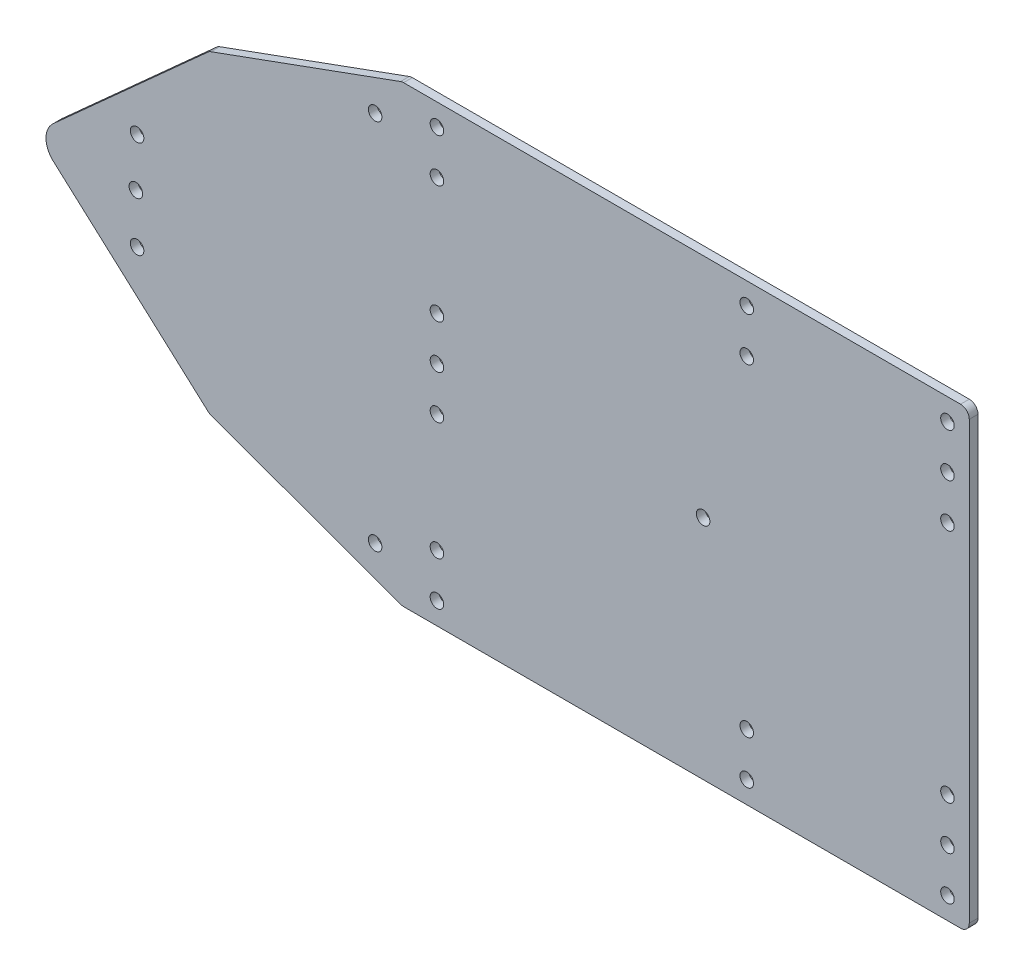
SolidWorks part; units mm, degrees
material "环氧板3240"
ref_plane "前视基准面" through (0, 0, 0) normal (0, 0, 1) x (1, 0, 0)
ref_plane "上视基准面" through (0, 0, 0) normal (0, 1, 0) x (1, 0, 0)
ref_plane "右视基准面" through (0, 0, 0) normal (1, 0, 0) x (0, 0, -1)
other "Configuration Table"
sketch "草图1" plane through (0, 0, 0) normal (0, 0, 1) x (1, 0, 0)
  line L0 (387.2013, -62.8358) -> (387.2013, 41.1642)
  line L1 (387.2013, 41.1642) -> (257.2013, 41.1642)
  line L2 (257.2013, 41.1642) -> (213.0357, 25.0892)
  line L4 (173.1369, -10.8358) -> (387.2013, -10.8358) construction
  line L5 (387.2013, -62.8358) -> (257.2013, -62.8358)
  line L6 (257.2013, -62.8358) -> (213.0357, -46.7609)
  line L8 (213.0357, 25.0892) -> (173.1369, -10.8358)
  line L9 (173.1369, -10.8358) -> (213.0357, -46.7609)
  dimension "D1" = 104
  dimension "D2" = 130
  dimension "D3" = 47
  dimension "D4" = 158
  dimension "D5" = 160
extrude "凸台-拉伸1" add sketch "草图1" along normal blind 2
fillet "圆角1" radius 5 1 edges at (173.1369, -10.8358, 1)
fillet "圆角2" radius 2 6 edges at (387.2013, 41.1642, 1) (257.2013, 41.1642, 1) (213.0357, 25.0892, 1) (213.0357, -46.7609, 1) (257.2013, -62.8358, 1) (387.2013, -62.8358, 1)
sketch "草图2" plane through (0, 0, 0) normal (0, 0, -1) x (-1, 0, 0)
  line L0 (-387.2013, 36.1642) -> (-243.4639, 36.1642) construction
  line L1 (-387.2013, -60.8358) -> (-387.2013, 39.1642) construction
  line L2 (-256.8699, 41.0436) -> (-213.401, 25.2222) construction
  line L3 (-385.2013, 41.1642) -> (-257.5539, 41.1642) construction
  line L4 (-387.2013, -10.8358) -> (-175.6093, -10.8358) construction
  line L5 (-382.2013, 36.1642) -> (-382.2013, -10.8358) construction
  line L6 (-258.541, 36.1642) -> (-177.1346, -10.8358) construction
  line L7 (-265.2013, 36.1642) -> (-265.2013, -10.8358) construction
  line L8 (-336.2013, 36.1642) -> (-336.2013, -10.8358) construction
  line L9 (-257.2013, 41.1642) -> (-183.864, -1.1771) construction
  line L10 (-251.041, 31.8341) -> (-248.541, 36.1642) construction
  line L11 (-212.7468, 24.8291) -> (-177.2636, -7.1201) construction
  circle A1 centre (-265.2013, 36.1642) radius 1.55
  circle A2 centre (-251.041, 31.8341) radius 1.55
  arc A3 (-177.2636, -14.5515) -> (-177.2636, -7.1201) centre (-180.6093, -10.8358) ccw construction
  circle A4 centre (-336.2013, 26.1642) radius 1.55
  circle A6 centre (-265.2013, 26.1642) radius 1.55
  circle A7 centre (-265.2013, -0.8358) radius 1.55
  circle A10 centre (-382.2013, 36.1642) radius 1.55
  circle A11 centre (-382.2013, 26.1642) radius 1.55
  circle A12 centre (-196.4814, 0.3341) radius 1.55
  circle A13 centre (-326.2013, -10.8358) radius 1.55
  circle A14 centre (-196.2013, -10.8358) radius 1.55
  circle A15 centre (-196.4814, -22.0057) radius 1.55
  circle A16 centre (-265.2013, -20.8358) radius 1.55
  circle A17 centre (-265.2013, -57.8358) radius 1.55
  circle A18 centre (-265.2013, -47.8358) radius 1.55
  circle A19 centre (-336.2013, -47.8358) radius 1.55
  circle A20 centre (-382.2013, -47.8358) radius 1.55
  circle A21 centre (-382.2013, -57.8358) radius 1.55
  circle A22 centre (-265.2013, -10.8358) radius 1.55
  circle A23 centre (-336.2013, 36.1642) radius 1.55
  circle A24 centre (-336.2013, -57.8358) radius 1.55
  circle A25 centre (-251.041, -53.5057) radius 1.55
  circle A26 centre (-382.2013, 16.1642) radius 1.55
  circle A27 centre (-382.2013, -37.8358) radius 1.55
  dimension "D3" = 3.1
  dimension "D4" = 10
  dimension "D5" = 117
  dimension "D6" = 63
  dimension "D9" = 15
  dimension "D11" = 20
  dimension "D12" = 10
  dimension "D13" = 130
  dimension "D17" = 10
  dimension "D1" = 5
  dimension "D2" = 5
  dimension "D7" = 46
  dimension "D8" = 150
  dimension "D10" = 56
  dimension "D14" = 130
  dimension "D15" = 5
  dimension "D16" = 10
extrude "切除-拉伸1" cut sketch "草图2" against normal blind 2
